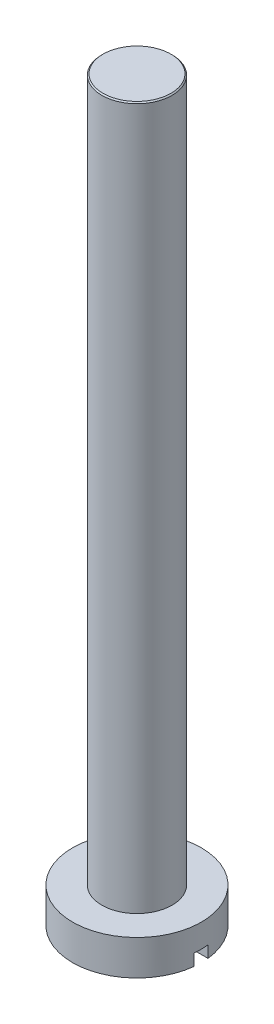
SolidWorks part; units mm, degrees
material "AISI 1045 Acero estirado en frío"
ref_plane "Front Plane" through (0, 0, 0) normal (0, 0, 1) x (1, 0, 0)
ref_plane "Top Plane" through (0, 0, 0) normal (0, 1, 0) x (1, 0, 0)
ref_plane "Right Plane" through (0, 0, 0) normal (1, 0, 0) x (0, 0, -1)
sketch "Sketch1" plane through (0, 0, 0) normal (0, 1, 0) x (1, 0, 0)
  circle A0 centre (0, 0) radius 1.5
  dimension "D1" = 3
extrude "Boss-Extrude1" add sketch "Sketch1" along normal blind 30
cosmetic thread "Cosmetic Thread1" parameters "D1"=11, "D2"=2.439
sketch "Sketch2" plane through (0, 0, 0) normal (0, -1, 0) x (1, 0, 0)
  circle A0 centre (0, 0) radius 2.75
  circle A1 centre (0, 0) radius 1.5
  circle A2 centre (0, 0) radius 1.5 construction
  dimension "D1" = 0
  dimension "D2" = 1.25
extrude "Boss-Extrude2" add sketch "Sketch2" along normal blind 1.5 separate body
sketch "Sketch3" plane through (0, -1.5, 0) normal (0, -1, 0) x (1, 0, 0)
  line L1 (-4.0982, -0.3) -> (4.0982, -0.3)
  line L2 (-4.0982, -0.3) -> (-4.0982, 0.3)
  line L3 (-4.0982, 0.3) -> (4.0982, 0.3)
  line L4 (4.0982, -0.3) -> (4.0982, 0.3)
  line L5 (-4.0982, -0.3) -> (4.0982, 0.3) construction
  line L6 (-4.0982, 0.3) -> (4.0982, -0.3) construction
  point P0 (0, 0)
  dimension "D1" = 0.6
extrude "Cut-Extrude1" cut sketch "Sketch3" against normal blind 0.5
chamfer "Chamfer1" distance 0.05 angle 45 1 edges at (0, 30, 1.5)
